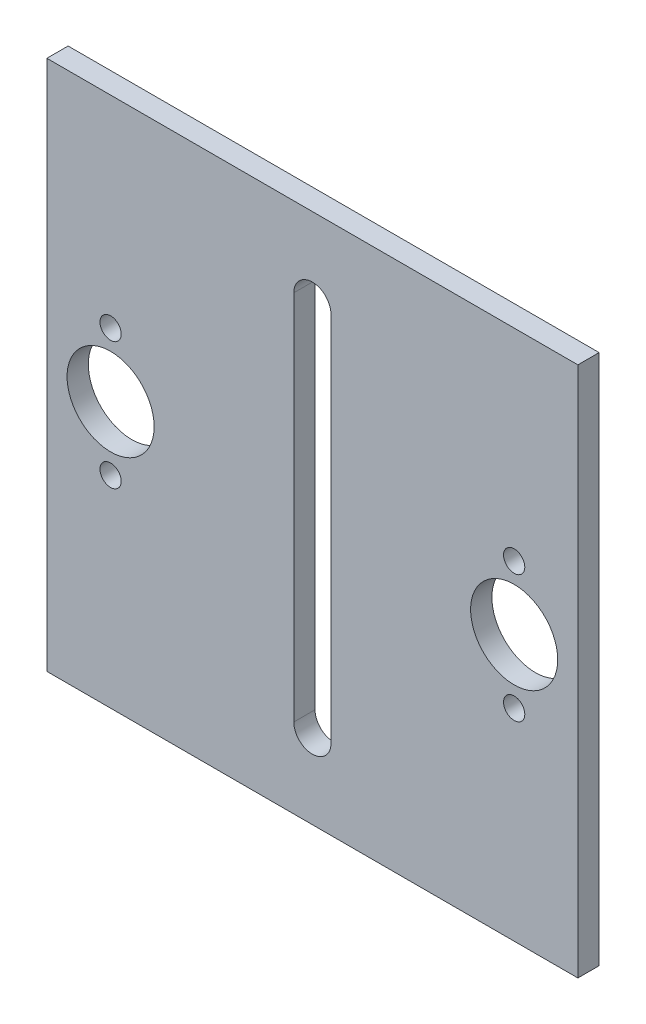
SolidWorks part; units mm, degrees
ref_plane "Front Plane" through (0, 0, 0) normal (0, 0, 1) x (1, 0, 0)
ref_plane "Top Plane" through (0, 0, 0) normal (0, 1, 0) x (1, 0, 0)
ref_plane "Right Plane" through (0, 0, 0) normal (1, 0, 0) x (0, 0, -1)
sketch "Sketch1" plane through (0, 0, 0) normal (0, 0, 1) x (1, 0, 0)
  line L1 (0, 0) -> (50, 0)
  line L2 (0, 0) -> (0, 50)
  line L3 (0, 50) -> (50, 50)
  line L4 (50, 0) -> (50, 50)
  dimension "D1" = 50
  dimension "D2" = 50
extrude "plate_body" add sketch "Sketch1" along normal blind 2
sketch "Sketch2" plane through (0, 0, 2) normal (0, 0, 1) x (1, 0, 0)
  line L0 (50, 50) -> (0, 50) construction
  line L1 (0, 50) -> (0, 0) construction
  circle A0 centre (6, 25) radius 4.1
  circle A1 centre (44, 25) radius 4.1
  dimension "D1" = 38
  dimension "D2" = 8.2
  dimension "D3" = 8.2
  dimension "D4" = 25
  dimension "D5" = 6
  dimension "D6" = 25
extrude "shaft_bearings" cut sketch "Sketch2" against normal through all
sketch "Sketch3" plane through (0, 0, 2) normal (0, 0, 1) x (1, 0, 0)
  line L0 (0, 50) -> (0, 0) construction
  line L1 (0, 50) -> (0, 0) construction
  line L2 (50, 0) -> (50, 50) construction
  circle A0 centre (6, 31) radius 1
  circle A1 centre (6, 19) radius 1
  circle A2 centre (44, 31) radius 1
  circle A3 centre (44, 19) radius 1
  circle A4 centre (6, 25) radius 4.1 construction
  circle A5 centre (44, 25) radius 4.1 construction
  dimension "D1" = 2
  dimension "D2" = 2
  dimension "D3" = 6
  dimension "D4" = 6
  dimension "D5" = 12
  dimension "D6" = 6
  dimension "D7" = 2
  dimension "D8" = 2
  dimension "D9" = 12
  dimension "D10" = 6
  dimension "D11" = 6
  dimension "D12" = 6
extrude "bearing_bolt_holes" cut sketch "Sketch3" against normal through all
sketch "Sketch4" plane through (0, 0, 2) normal (0, 0, 1) x (1, 0, 0)
  line L0 (25, 42.5) -> (25, 7.5) construction
  line L1 (26.75, 42.5) -> (26.75, 7.5)
  line L2 (23.25, 42.5) -> (23.25, 7.5)
  line L3 (0, 50) -> (0, 0) construction
  line L4 (0, 0) -> (50, 0) construction
  arc A0 (26.75, 42.5) -> (23.25, 42.5) centre (25, 42.5) ccw
  arc A1 (23.25, 7.5) -> (26.75, 7.5) centre (25, 7.5) ccw
  point P2 (25, 25)
  dimension "D4" = 7.5
  dimension "D1" = 3.5
  dimension "D2" = 35
  dimension "D3" = 25
extrude "Cut-Extrude1" cut sketch "Sketch4" against normal through all
